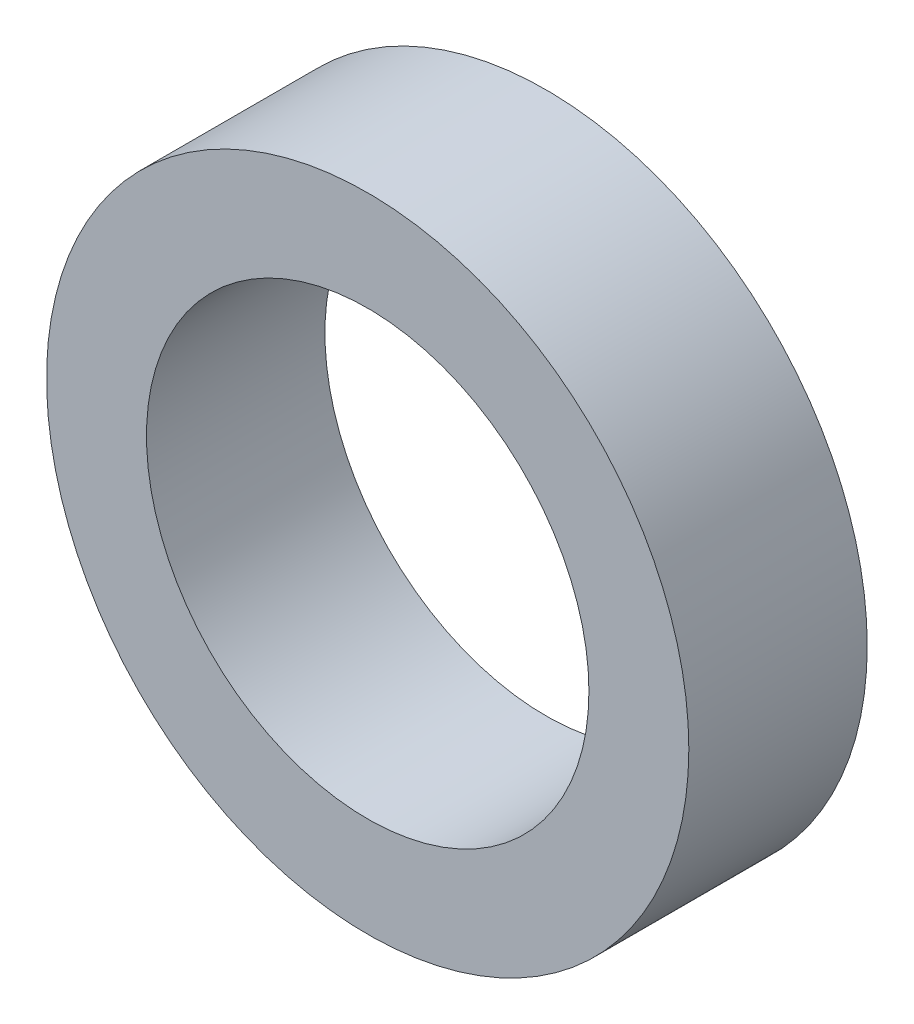
SolidWorks part; units mm, degrees
ref_plane "Front Plane" through (0, 0, 0) normal (0, 0, 1) x (1, 0, 0)
ref_plane "Top Plane" through (0, 0, 0) normal (0, 1, 0) x (1, 0, 0)
ref_plane "Right Plane" through (0, 0, 0) normal (1, 0, 0) x (0, 0, -1)
sketch "Sketch1" plane through (0, 0, 0) normal (0, 0, 1) x (1, 0, 0)
  circle A0 centre (0, 0) radius 9
  circle A1 centre (0, 0) radius 6.2
  point P4 (0, 0)
extrude "Boss-Extrude1" add sketch "Sketch1" along normal blind 5
